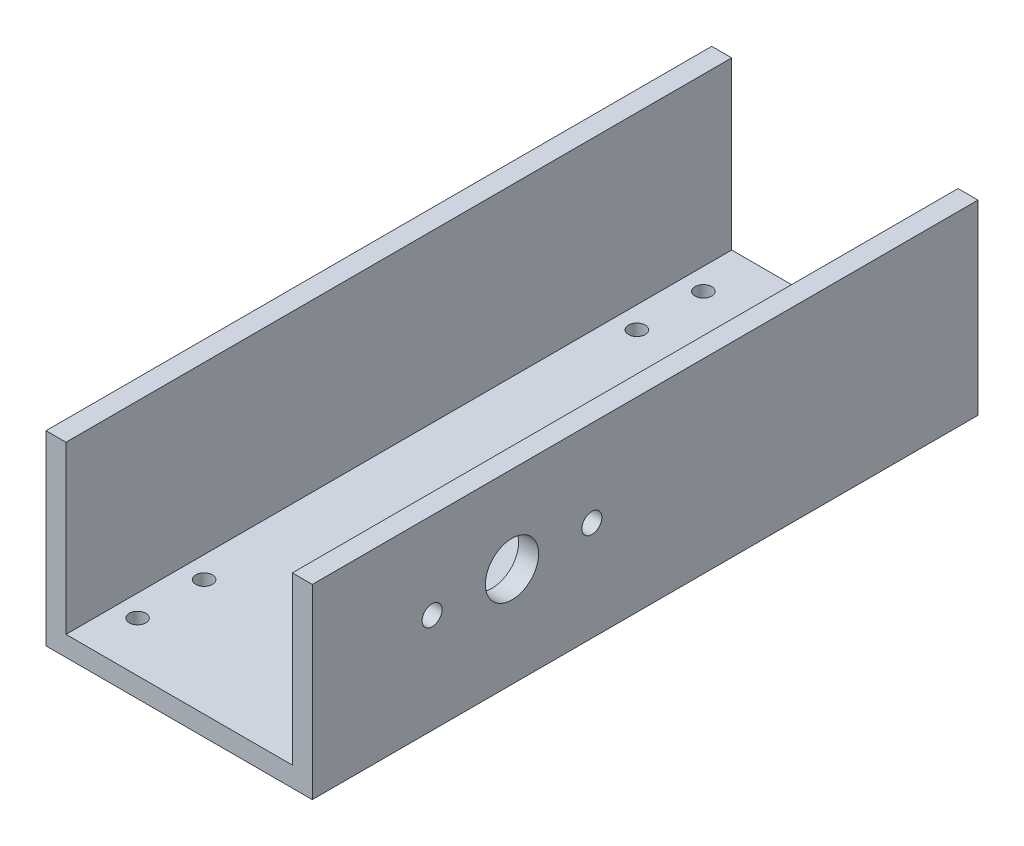
SolidWorks part; units mm, degrees
material "6061 合金"
ref_plane "前视基准面" through (0, 0, 0) normal (0, 0, 1) x (1, 0, 0)
ref_plane "上视基准面" through (0, 0, 0) normal (0, 1, 0) x (1, 0, 0)
ref_plane "右视基准面" through (0, 0, 0) normal (1, 0, 0) x (0, 0, -1)
sketch "草图1" plane through (0, 0, 0) normal (0, 0, 1) x (1, 0, 0)
  line L0 (0, 0) -> (0, 56.8781) construction
  line L1 (-40, 0) -> (40, 0)
  line L2 (40, 0) -> (40, 56)
  line L3 (40, 56) -> (34, 56)
  line L4 (34, 56) -> (34, 6)
  line L5 (34, 6) -> (-34, 6)
  line L6 (-40, 0) -> (-40, 56)
  line L7 (-40, 56) -> (-34, 56)
  line L8 (-34, 56) -> (-34, 6)
  point P8 (0, 6)
  dimension "D1" = 80
  dimension "D2" = 6
  dimension "D3" = 6
  dimension "D4" = 50
  dimension "D5" = 6
extrude "凸台-拉伸1" add sketch "草图1" along normal blind 200
sketch "草图3" plane through (40, 0, 0) normal (1, 0, 0) x (0, 0, -1)
  line L0 (-200, 30) -> (-140, 30) construction
  line L2 (-164, 37.2595) -> (-164, 30) construction
  line L3 (-140, 30) -> (-140, 59.236) construction
  line L4 (-200, 0) -> (0, 0) construction
  line L5 (-200, 0) -> (-200, 56) construction
  circle A0 centre (-140, 30) radius 8
  circle A1 centre (-164, 30) radius 3
  circle A2 centre (-116, 30) radius 3
  point P13 (-233.7509, 28.9439)
  dimension "D1" = 60
  dimension "D2" = 6
  dimension "D4" = 16
  dimension "D5" = 30
  dimension "D3" = 24
extrude "切除-拉伸1" cut sketch "草图3" against normal up to next contours A0 | A1 | A2
sketch "草图4" plane through (0, 0, 0) normal (0, -1, 0) x (1, 0, 0)
  line L0 (27.5, 165) -> (27.5, 185) construction
  line L1 (27.5, 165) -> (-27.5, 165) construction
  line L2 (27.5, 185) -> (-27.5, 185) construction
  line L3 (-27.5, 165) -> (-27.5, 185) construction
  line L4 (27.5, 165) -> (-27.5, 185) construction
  line L5 (27.5, 185) -> (-27.5, 165) construction
  line L6 (0, 200) -> (0, 139.8429) construction
  line L7 (-40, 200) -> (40, 200) construction
  line L8 (-40, 100) -> (40, 100) construction
  line L9 (-40, 200) -> (-40, 0) construction
  line L10 (40, 200) -> (40, 0) construction
  line L11 (0, 0) -> (0, 60.1571) construction
  line L12 (27.5, 15) -> (-27.5, 35) construction
  line L13 (27.5, 35) -> (-27.5, 15) construction
  line L14 (-27.5, 35) -> (-27.5, 15) construction
  line L15 (27.5, 15) -> (-27.5, 15) construction
  line L16 (27.5, 35) -> (-27.5, 35) construction
  line L17 (27.5, 35) -> (27.5, 15) construction
  circle A0 centre (-27.5, 185) radius 2.5
  circle A1 centre (27.5, 185) radius 2.5
  circle A2 centre (-27.5, 165) radius 2.5
  circle A3 centre (27.5, 165) radius 2.5
  circle A4 centre (27.5, 35) radius 2.5
  circle A5 centre (-27.5, 35) radius 2.5
  circle A6 centre (27.5, 15) radius 2.5
  circle A7 centre (-27.5, 15) radius 2.5
  point P1 (0, 175)
  point P29 (0, 25)
  dimension "D4" = 5
  dimension "D5" = 5
  dimension "D6" = 5
  dimension "D7" = 5
  dimension "D1" = 55
  dimension "D2" = 15
  dimension "D3" = 20
extrude "切除-拉伸2" cut sketch "草图4" against normal up to next
